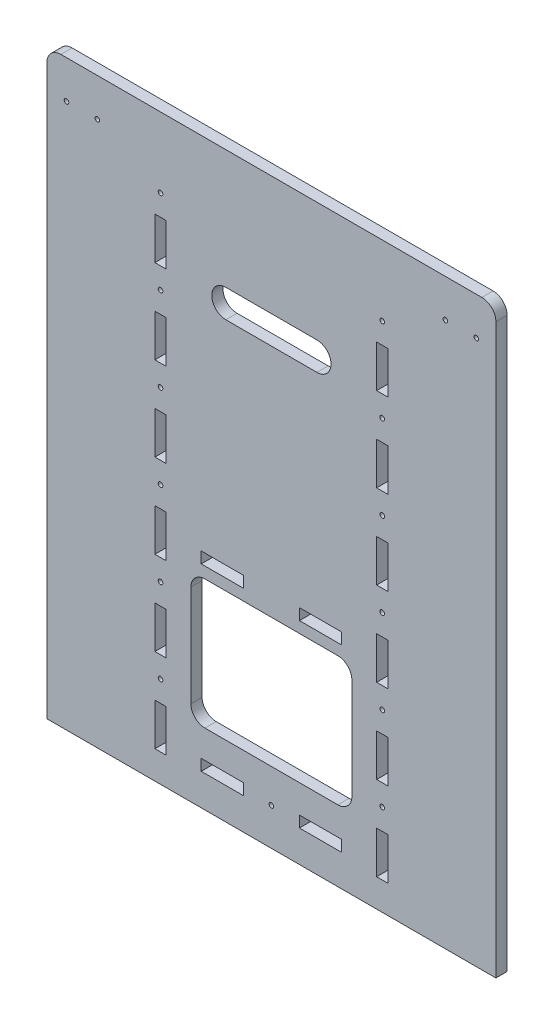
SolidWorks part; units mm, degrees
material "Acrylic (Medium-high impact)"
ref_plane "Front Plane" through (0, 0, 0) normal (0, 0, 1) x (1, 0, 0)
ref_plane "Top Plane" through (0, 0, 0) normal (0, 1, 0) x (1, 0, 0)
ref_plane "Right Plane" through (0, 0, 0) normal (1, 0, 0) x (0, 0, -1)
sketch "Sketch1" plane through (0, 0, 0) normal (0, 0, 1) x (1, 0, 0)
  line L0 (112.646, 142.6024) -> (207.354, 142.6024)
  line L1 (0, 0) -> (320, 0)
  line L2 (0, 0) -> (0, 415)
  line L3 (160, 375.6395) -> (160, 0) construction
  line L4 (320, 0) -> (320, 415)
  line L6 (217.354, 132.6024) -> (217.354, 60.5669)
  line L7 (85, 50) -> (77, 50)
  line L8 (160, 415) -> (0, 415)
  line L9 (207.354, 50.5669) -> (112.646, 50.5669)
  line L10 (160, 415) -> (320, 415)
  line L11 (102.646, 132.6024) -> (102.646, 60.5669)
  line L12 (85, 50) -> (85, 20)
  line L13 (85, 20) -> (77, 20)
  line L14 (77, 50) -> (77, 20)
  line L19 (210, 30.5669) -> (180, 30.5669)
  line L20 (210, 30.5669) -> (210, 22.5669)
  line L21 (210, 22.5669) -> (180, 22.5669)
  line L22 (180, 30.5669) -> (180, 22.5669)
  line L23 (110, 30.5669) -> (140, 30.5669)
  line L24 (110, 30.5669) -> (110, 22.5669)
  line L25 (110, 22.5669) -> (140, 22.5669)
  line L26 (140, 30.5669) -> (140, 22.5669)
  line L27 (110, 158.5669) -> (140, 158.5669)
  line L28 (110, 158.5669) -> (110, 150.5669)
  line L29 (110, 150.5669) -> (140, 150.5669)
  line L30 (140, 158.5669) -> (140, 150.5669)
  line L31 (180, 158.5669) -> (210, 158.5669)
  line L32 (180, 158.5669) -> (180, 150.5669)
  line L33 (180, 150.5669) -> (210, 150.5669)
  line L34 (210, 158.5669) -> (210, 150.5669)
  line L67 (243, 20) -> (235, 20)
  line L68 (243, 50) -> (243, 20)
  line L69 (235, 50) -> (235, 20)
  line L70 (243, 50) -> (235, 50)
  line L71 (85, 80) -> (77, 80)
  line L72 (85, 110) -> (85, 80)
  line L73 (77, 110) -> (77, 80)
  line L74 (85, 110) -> (77, 110)
  line L75 (243, 80) -> (235, 80)
  line L76 (243, 110) -> (243, 80)
  line L77 (235, 110) -> (235, 80)
  line L78 (243, 110) -> (235, 110)
  line L79 (85, 140) -> (77, 140)
  line L80 (85, 170) -> (85, 140)
  line L81 (77, 170) -> (77, 140)
  line L82 (85, 170) -> (77, 170)
  line L83 (243, 140) -> (235, 140)
  line L84 (243, 170) -> (243, 140)
  line L85 (235, 170) -> (235, 140)
  line L86 (243, 170) -> (235, 170)
  line L87 (85, 200) -> (77, 200)
  line L88 (85, 230) -> (85, 200)
  line L89 (77, 230) -> (77, 200)
  line L90 (85, 230) -> (77, 230)
  line L91 (243, 200) -> (235, 200)
  line L92 (243, 230) -> (243, 200)
  line L93 (235, 230) -> (235, 200)
  line L94 (243, 230) -> (235, 230)
  line L95 (85, 260) -> (77, 260)
  line L96 (85, 290) -> (85, 260)
  line L97 (77, 290) -> (77, 260)
  line L98 (85, 290) -> (77, 290)
  line L99 (243, 260) -> (235, 260)
  line L100 (243, 290) -> (243, 260)
  line L101 (235, 290) -> (235, 260)
  line L102 (243, 290) -> (235, 290)
  line L103 (85, 320) -> (77, 320)
  line L104 (85, 350) -> (85, 320)
  line L105 (77, 350) -> (77, 320)
  line L106 (85, 350) -> (77, 350)
  line L107 (243, 320) -> (235, 320)
  line L108 (243, 350) -> (243, 320)
  line L109 (235, 350) -> (235, 320)
  line L110 (243, 350) -> (235, 350)
  circle A0 centre (14, 388) radius 1.625
  circle A1 centre (36, 388) radius 1.625
  arc A2 (217.354, 60.5669) -> (207.354, 50.5669) centre (207.354, 60.5669) cw
  arc A3 (207.354, 142.6024) -> (217.354, 132.6024) centre (207.354, 132.6024) cw
  circle A4 centre (284, 388) radius 1.625
  circle A5 centre (306, 388) radius 1.625
  arc A6 (112.646, 142.6024) -> (102.646, 132.6024) centre (112.646, 132.6024) ccw
  arc A7 (102.646, 60.5669) -> (112.646, 50.5669) centre (112.646, 60.5669) ccw
  circle A8 centre (81, 65) radius 1.65
  circle A9 centre (239, 65) radius 1.65
  circle A10 centre (81, 125) radius 1.65
  circle A11 centre (239, 125) radius 1.65
  circle A12 centre (81, 185) radius 1.65
  circle A13 centre (239, 185) radius 1.65
  circle A14 centre (81, 245) radius 1.65
  circle A15 centre (239, 245) radius 1.65
  circle A16 centre (81, 305) radius 1.65
  circle A17 centre (239, 305) radius 1.65
  circle A18 centre (81, 365) radius 1.65
  circle A19 centre (239, 365) radius 1.65
  circle A20 centre (160, 26.5669) radius 1.65
  point P27 (160, 142.6024)
  point P37 (160, 50.5669)
  dimension "D6" = 10
  dimension "D8" = 20
  dimension "D7" = 22
  dimension "D9" = 27
  dimension "D4" = 3.25
  dimension "D5" = 3.25
  dimension "D16" = 6
  dimension "D17" = 3.3
  dimension "D2" = 320
  dimension "D3" = 415
  dimension "D10" = 124
  dimension "D11" = 75
  dimension "D13" = 2
  dimension "D14" = 6
  dimension "D15" = 30
  dimension "D18" = 6
  dimension "D12" = 8
extrude "Boss-Extrude1" add sketch "Sketch1" along normal blind 8
fillet "Fillet1" radius 10 2 edges at (320, 415, 4) (0, 415, 4)
sketch "Sketch2" plane through (0, 0, 0) normal (0, 0, -1) x (-1, 0, 0)
  line L0 (-160, 415) -> (-160, 0) construction
  line L1 (-310, 415) -> (-10, 415) construction
  line L2 (0, 0) -> (-320, 0) construction
  line L3 (-192.5, 320) -> (-127.5, 320) construction
  line L4 (-192.5, 330) -> (-127.5, 330)
  line L5 (-192.5, 310) -> (-127.5, 310)
  arc A0 (-192.5, 330) -> (-192.5, 310) centre (-192.5, 320) ccw
  arc A1 (-127.5, 310) -> (-127.5, 330) centre (-127.5, 320) ccw
  point P8 (-160, 320)
  dimension "D2" = 10
  dimension "D1" = 65
  dimension "D3" = 320
extrude "Cut-Extrude1" cut sketch "Sketch2" against normal through all
